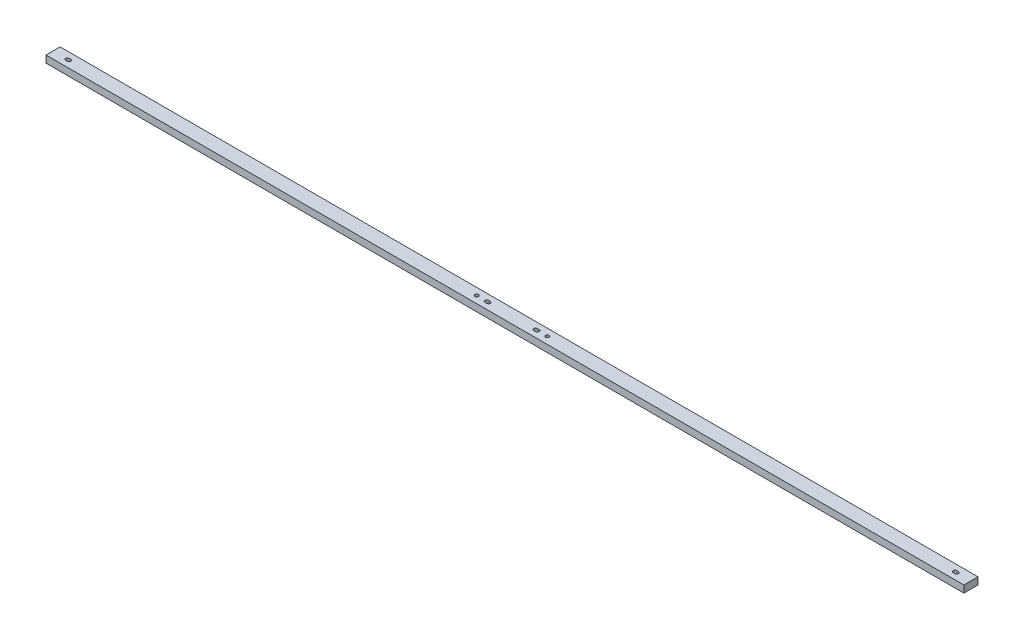
SolidWorks part; units mm, degrees
ref_plane "Front Plane" through (0, 0, 0) normal (0, 0, 1) x (1, 0, 0)
ref_plane "Top Plane" through (0, 0, 0) normal (0, 1, 0) x (1, 0, 0)
ref_plane "Right Plane" through (0, 0, 0) normal (1, 0, 0) x (0, 0, -1)
sketch "Sketch1" plane through (0, 0, 0) normal (0, 1, 0) x (1, 0, 0)
  line L0 (-799.6555, 0) -> (-796.4805, 0) construction
  line L1 (-825.5, 12.7) -> (825.5, 12.7)
  line L2 (-825.5, 12.7) -> (-825.5, -12.7)
  line L3 (-825.5, -12.7) -> (825.5, -12.7)
  line L4 (825.5, 12.7) -> (825.5, -12.7)
  line L5 (-825.5, 12.7) -> (825.5, -12.7) construction
  line L6 (-825.5, -12.7) -> (825.5, 12.7) construction
  line L7 (-799.6555, 3.175) -> (-796.4805, 3.175)
  line L8 (-799.6555, -3.175) -> (-796.4805, -3.175)
  line L9 (0, 181.749) -> (0, -181.749) construction
  line L10 (45.5295, 0) -> (42.3545, 0) construction
  line L13 (-45.5295, 0) -> (-42.3545, 0) construction
  line L14 (-45.5295, 3.175) -> (-42.3545, 3.175)
  line L15 (-45.5295, -3.175) -> (-42.3545, -3.175)
  line L16 (45.5295, 3.175) -> (42.3545, 3.175)
  line L17 (45.5295, -3.175) -> (42.3545, -3.175)
  line L18 (799.6555, 0) -> (796.4805, 0) construction
  line L19 (799.6555, 3.175) -> (796.4805, 3.175)
  line L20 (799.6555, -3.175) -> (796.4805, -3.175)
  line L21 (825.5, 0) -> (-825.5, 0) construction
  arc A0 (-799.6555, 3.175) -> (-799.6555, -3.175) centre (-799.6555, 0) ccw
  arc A1 (-796.4805, -3.175) -> (-796.4805, 3.175) centre (-796.4805, 0) ccw
  arc A4 (-45.5295, 3.175) -> (-45.5295, -3.175) centre (-45.5295, 0) ccw
  arc A5 (-42.3545, -3.175) -> (-42.3545, 3.175) centre (-42.3545, 0) ccw
  arc A6 (45.5295, 3.175) -> (45.5295, -3.175) centre (45.5295, 0) cw
  arc A7 (42.3545, -3.175) -> (42.3545, 3.175) centre (42.3545, 0) cw
  arc A8 (799.6555, 3.175) -> (799.6555, -3.175) centre (799.6555, 0) cw
  arc A9 (796.4805, -3.175) -> (796.4805, 3.175) centre (796.4805, 0) cw
  circle A10 centre (63.5, 0) radius 3.175
  circle A11 centre (-63.5, 0) radius 3.175
  point P0 (0, 0)
  point P8 (-798.068, 0)
  point P16 (0, 0)
  point P18 (43.942, 0)
  point P25 (-43.942, 0)
  point P32 (798.068, 0)
  dimension "D3" = 3.175
  dimension "D7" = 63.5
  dimension "D8" = 6.35
  dimension "D1" = 25.4
  dimension "D2" = 1651
  dimension "D4" = 3.175
  dimension "D5" = 27.432
  dimension "D6" = 754.126
extrude "Boss-Extrude1" add sketch "Sketch1" along normal blind 12.7
